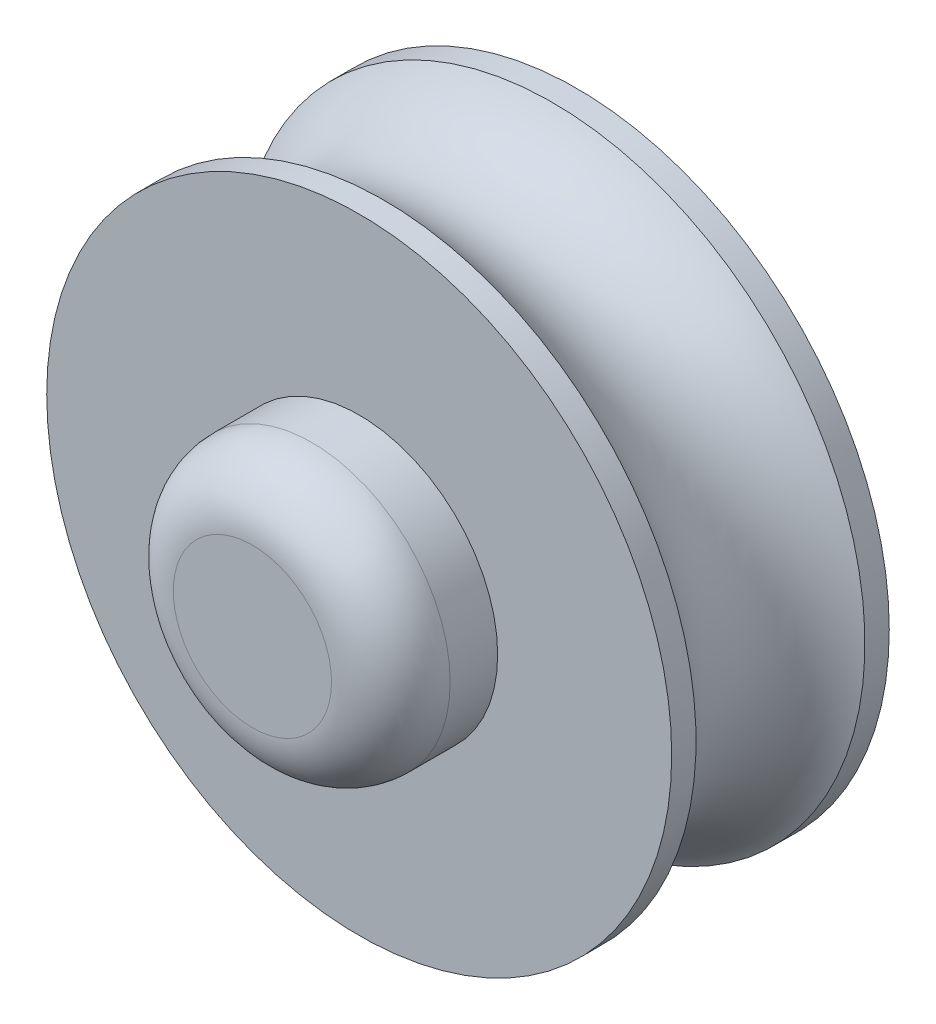
SolidWorks part; units mm, degrees
ref_plane "정면" through (0, 0, 0) normal (0, 0, 1) x (1, 0, 0)
ref_plane "윗면" through (0, 0, 0) normal (0, 1, 0) x (1, 0, 0)
ref_plane "우측면" through (0, 0, 0) normal (1, 0, 0) x (0, 0, -1)
sketch "스케치1" plane through (0, 0, 0) normal (0, 0, 1) x (1, 0, 0)
  circle A0 centre (0, 0) radius 7.9
  dimension "D1" = 15.8
extrude "보스-돌출1" add sketch "스케치1" along normal blind 5.5
sketch "스케치2" plane through (0, 0, 5.5) normal (0, 0, 1) x (1, 0, 0)
  circle A0 centre (0, 0) radius 3.5
  dimension "D1" = 7
extrude "보스-돌출2" add sketch "스케치2" along normal blind 2.7
sketch "스케치6" plane through (0, 0, 0) normal (1, 0, 0) x (0, 0, -1)
  line L0 (0, -7.9) -> (1.3033, -3.5)
  line L1 (1.3033, -3.5) -> (1.3033, 0)
  line L2 (0, 0) -> (4.5929, 0) construction
  line L3 (0, -7.9) -> (3.6625, -7.9) construction
  line L4 (0, 0) -> (1.3033, 0)
  line L5 (0, 0) -> (0, -7.9)
  dimension "D1" = 3.5
  dimension "D2" = 73.5
revolve "회전1" add sketch "스케치6" angle 360 about L2
sketch "스케치7" plane through (0, 0, -1.3033) normal (0, 0, -1) x (-1, 0, 0)
  line L0 (-1.02, 2.2617) -> (-1.02, -2.0653)
  circle A0 centre (0, 0) radius 1.6
  dimension "D2" = 3.2
  dimension "D1" = 1.02
extrude "컷-돌출1" cut sketch "스케치7" against normal blind 9.3 contours L0 A0
fillet "필렛1" radius 1.5 1 edges at (3.5, 0, 8.2)
sketch "스케치8" plane through (0, 0, 0) normal (1, 0, 0) x (0, 0, -1)
  line L0 (-5.5, 7.9) -> (-5.5, -7.9) construction
  line L1 (-4.885, 7.9) -> (-0.615, 7.9)
  line L2 (0, 0) -> (-10.7488, 0) construction
  arc A0 (-4.885, 7.9) -> (-0.615, 7.9) centre (-2.75, 9.2007) ccw
  dimension "D2" = 5
  dimension "D1" = 2.75
  dimension "D3" = 0.615
  dimension "D4" = 0.615
revolve "컷-회전1" cut sketch "스케치8" angle 360 about L2
